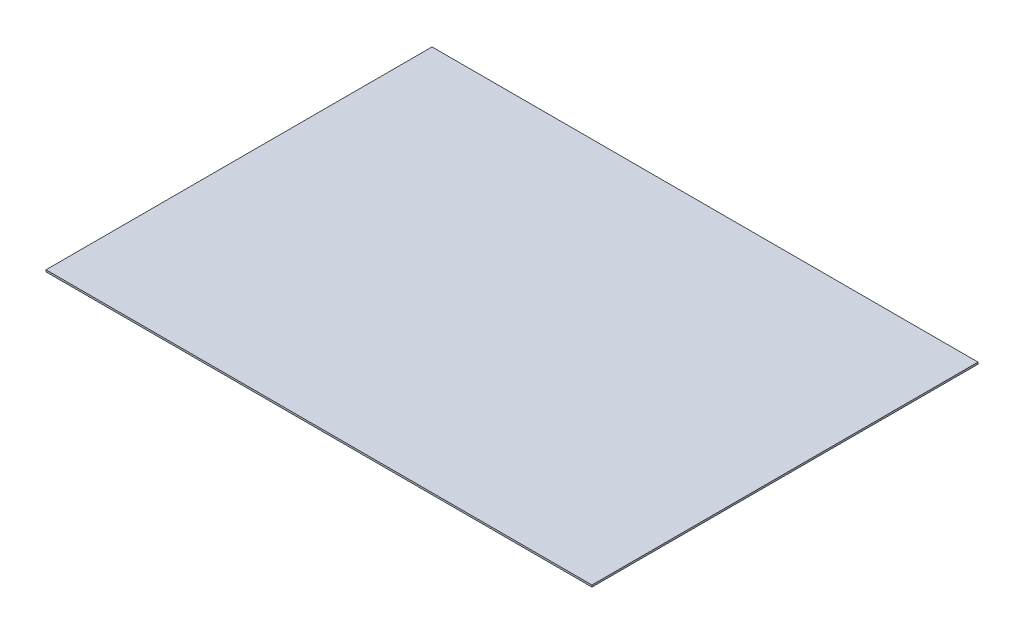
SolidWorks part; units mm, degrees
ref_plane "Front Plane" through (0, 0, 0) normal (0, 0, 1) x (1, 0, 0)
ref_plane "Top Plane" through (0, 0, 0) normal (0, 1, 0) x (1, 0, 0)
ref_plane "Right Plane" through (0, 0, 0) normal (1, 0, 0) x (0, 0, -1)
sketch "Sketch1" plane through (0, 0, 0) normal (0, 1, 0) x (1, 0, 0)
  line L1 (-152.4425, 93.0863) -> (144.5575, 93.0863)
  line L2 (-152.4425, 93.0863) -> (-152.4425, -116.9137)
  line L3 (-152.4425, -116.9137) -> (144.5575, -116.9137)
  line L4 (144.5575, 93.0863) -> (144.5575, -116.9137)
  dimension "D1" = 297
  dimension "D2" = 210
extrude "Boss-Extrude1" add sketch "Sketch1" along normal blind 1
